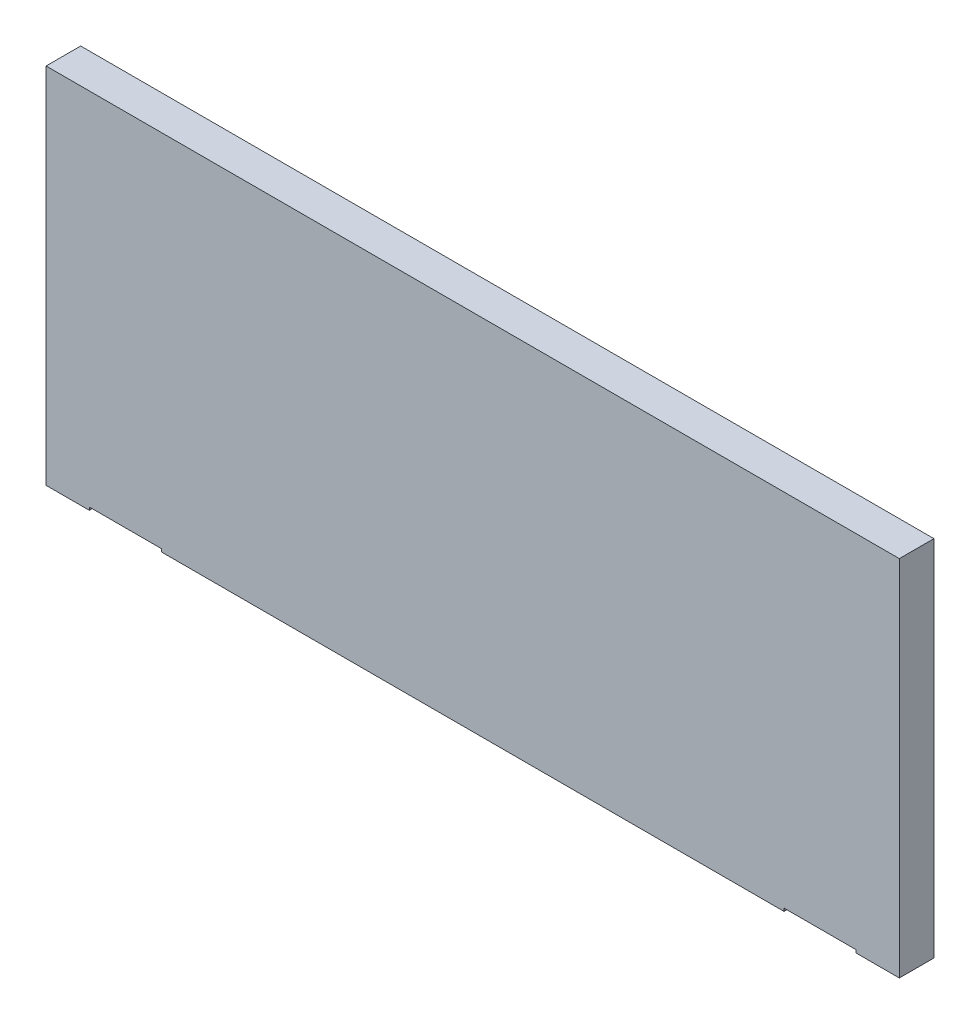
SolidWorks part; units mm, degrees
ref_plane "Front Plane" through (0, 0, 0) normal (0, 0, 1) x (1, 0, 0)
ref_plane "Top Plane" through (0, 0, 0) normal (0, 1, 0) x (1, 0, 0)
ref_plane "Right Plane" through (0, 0, 0) normal (1, 0, 0) x (0, 0, -1)
sketch "Sketch1" plane through (0, 0, 0) normal (0, 0, 1) x (1, 0, 0)
  line L1 (0, 0) -> (296, 0)
  line L2 (0, 0) -> (0, 126)
  line L3 (0, 126) -> (296, 126)
  line L4 (296, 0) -> (296, 126)
  dimension "D1" = 126
  dimension "D2" = 296
extrude "Boss-Extrude1" add sketch "Sketch1" along normal blind 12
sketch "Sketch2" plane through (0, 0, 0) normal (0, 1, 0) x (1, 0, 0)
  line L0 (0, -6) -> (296, -6) construction
  line L1 (0, -12) -> (0, 0) construction
  line L2 (296, -12) -> (296, 0) construction
  circle A0 centre (21, -6) radius 1.5
  circle A1 centre (34, -6) radius 1.5
  circle A2 centre (275, -6) radius 1.5
  circle A3 centre (262, -6) radius 1.5
  dimension "D1" = 3
  dimension "D2" = 3
  dimension "D5" = 3
  dimension "D6" = 3
  dimension "D3" = 21
  dimension "D4" = 13
  dimension "D7" = 21
  dimension "D8" = 13
extrude "Cut-Extrude1" cut sketch "Sketch2" along normal blind 10
sketch "Sketch3" plane through (0, 0, 0) normal (0, 1, 0) x (1, 0, 0)
  line L0 (0, -12) -> (296, -12) construction
  line L1 (15, -12) -> (40, -12)
  line L2 (15, -12) -> (15, 0)
  line L3 (15, 0) -> (40, 0)
  line L4 (40, -12) -> (40, 0)
  line L5 (0, 0) -> (296, 0) construction
  line L7 (256, -12) -> (281, -12)
  line L8 (256, -12) -> (256, 0)
  line L9 (256, 0) -> (281, 0)
  line L10 (281, -12) -> (281, 0)
  dimension "D1" = 25
  dimension "D2" = 15
  dimension "D3" = 12
  dimension "D4" = 25
  dimension "D5" = 15
  dimension "D6" = 12
extrude "Cut-Extrude2" cut sketch "Sketch3" along normal blind 1
